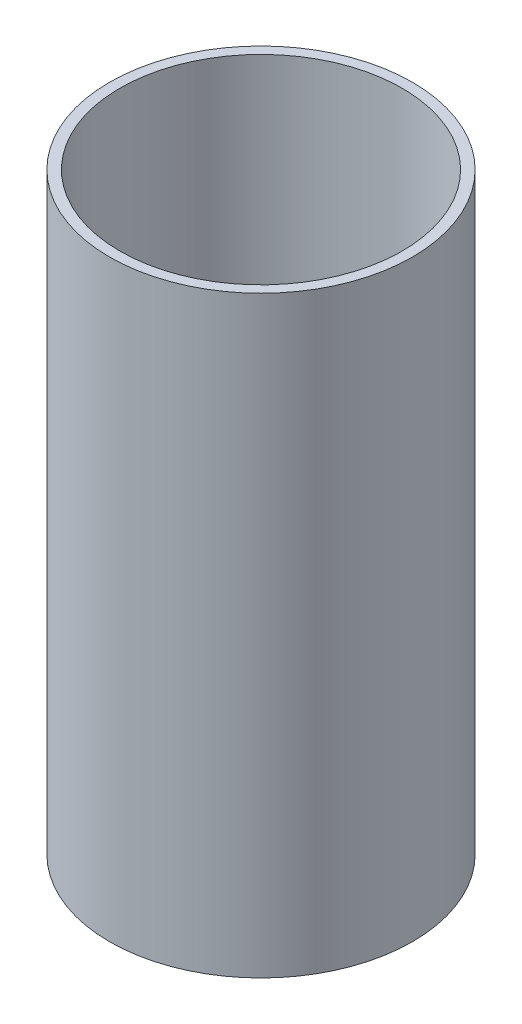
SolidWorks part; units mm, degrees
ref_plane "Front Plane" through (0, 0, 0) normal (0, 0, 1) x (1, 0, 0)
ref_plane "Top Plane" through (0, 0, 0) normal (0, 1, 0) x (1, 0, 0)
ref_plane "Right Plane" through (0, 0, 0) normal (1, 0, 0) x (0, 0, -1)
sketch "Sketch1" plane through (0, 0, 0) normal (0, 1, 0) x (1, 0, 0)
  circle A0 centre (0, 0) radius 17.85
  circle A1 centre (0, 0) radius 19.15
  dimension "D1" = 35.7
  dimension "D2" = 38.3
extrude "Boss-Extrude1" add sketch "Sketch1" along normal blind 75
